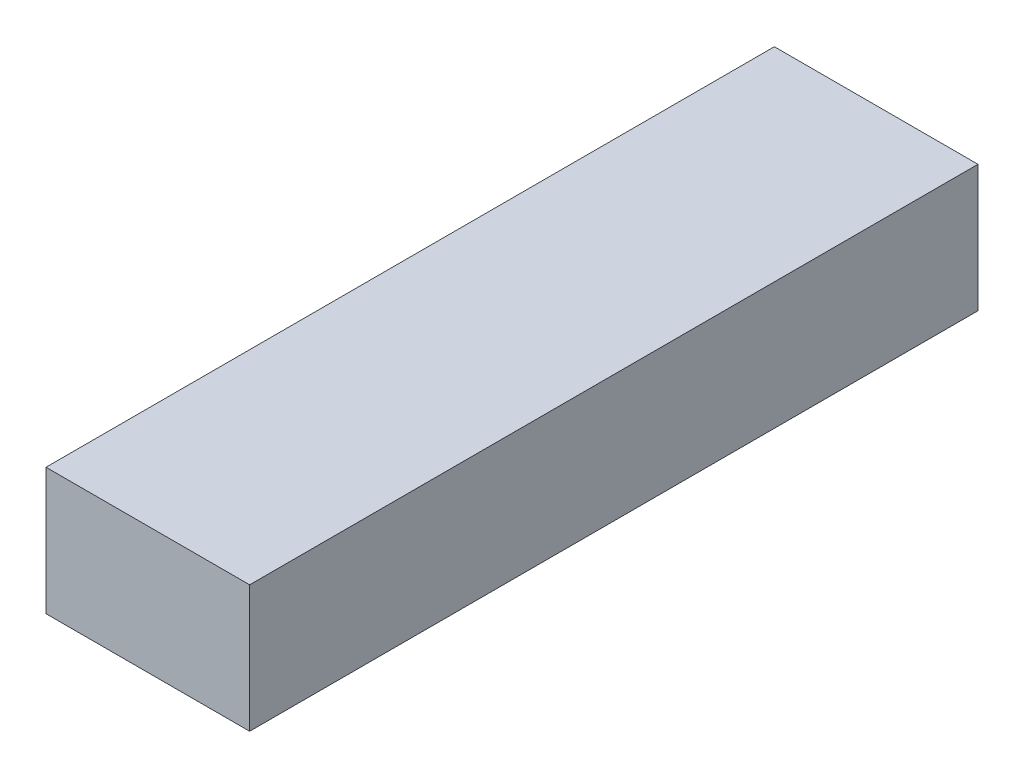
SolidWorks part; units mm, degrees
ref_plane "정면" through (0, 0, 0) normal (0, 0, 1) x (1, 0, 0)
ref_plane "윗면" through (0, 0, 0) normal (0, 1, 0) x (1, 0, 0)
ref_plane "우측면" through (0, 0, 0) normal (1, 0, 0) x (0, 0, -1)
sketch "스케치1" plane through (0, 0, 0) normal (0, 0, 1) x (1, 0, 0)
  line L0 (-26.5792, -46.75) -> (-26.5792, -67.65) construction
  line L1 (3.3458, -46.75) -> (-56.5042, -46.75) construction
  line L2 (-56.5042, -67.65) -> (3.3458, -67.65) construction
  line L3 (-56.5042, -57.2) -> (3.3458, -57.2) construction
  line L4 (-56.5042, -46.75) -> (-56.5042, -67.65) construction
  line L6 (-43.3542, -67.65) -> (-9.8042, -67.65)
  line L7 (-43.3542, -67.65) -> (-43.3542, -46.75)
  line L8 (-43.3542, -46.75) -> (-9.8042, -46.75)
  line L9 (-9.8042, -67.65) -> (-9.8042, -46.75)
  line L10 (-43.3542, -67.65) -> (-9.8042, -46.75) construction
  line L11 (-43.3542, -46.75) -> (-9.8042, -67.65) construction
  point P11 (-26.5792, -57.2)
  dimension "D1" = 33.55
extrude "보스-돌출1" add sketch "스케치1" along normal blind 120
